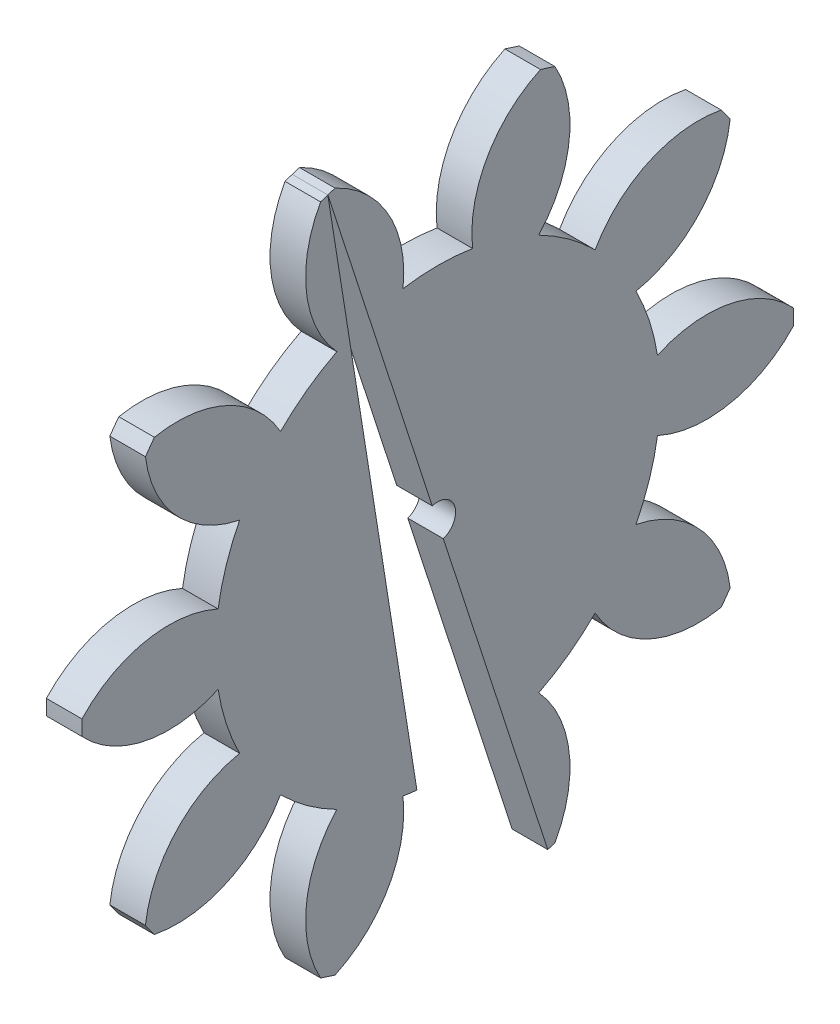
SolidWorks part; units mm, degrees
ref_plane "Plane1" through (0, 0, 0) normal (0, 0, 1) x (1, 0, 0)
ref_plane "Plane2" through (0, 0, 0) normal (0, 1, 0) x (1, 0, 0)
ref_plane "Plane3" through (0, 0, 0) normal (1, 0, 0) x (0, 0, -1)
sketch "HoldingSke" plane through (0, 0, 0) normal (0, 1, 0) x (1, 0, 0)
  line L0 (0, 0) -> (0.197, -0.0347)
  line L1 (-15, 0) -> (100, 0) construction
  line L2 (0, 0) -> (-2.1039, 2.3779)
  line L3 (0, 0) -> (-11.863, 4.5341)
  line L4 (0, 0) -> (8.5048, 1.4996)
  line L5 (0, 0) -> (-46.8476, -17.4728)
  line L6 (0, 0) -> (-2.4869, -1.6779)
  line L7 (-2.1039, 2.3779) -> (8.6586, 51.2059)
  line L8 (-76.2, 54.61) -> (-75.7, 54.61)
  line L9 (-71.009, 38.7566) -> (-53.1078, 45.2721)
  line L10 (-76.2, 71.12) -> (104.1128, 71.12)
  line L11 (0, 0) -> (-3, 0)
  line L12 (-76.2, 101.6) -> (-76.033, 101.6)
  line L13 (24.9733, 27.94) -> (52.9518, 28.4284)
  line L14 (24.9733, 27.94) -> (24.9743, 27.94)
  line L15 (24.9733, 27.94) -> (100.4006, 29.5858)
  line L16 (-63.627, -5) -> (-12.827, -5)
  circle A0 centre (0, 0) radius 1.5
  circle A1 centre (0, 0) radius 18.749
  circle A2 centre (0, 0) radius 37.5
  circle A3 centre (0, 0) radius 1.5
  dimension "MHD" = 37.498
  dimension "Hub_dia" = 75
  dimension "Bore" = 3
  dimension "MBD" = 3
  dimension "Num_teeth" = 10
  dimension "Pitch" = 0.2
  dimension "Overall_len" = 50
  dimension "Show_teeth" = 10
  dimension "Thickness" = 3
  dimension "OAL" = 50.0001
  dimension "T_dim" = 0.5
  dimension "Ap" = 20
  dimension "H" = 19.05
  dimension "Pitch_radius" = 180.3128
  dimension "Width" = 3
  dimension "Backlash" = 0.167
  dimension "Addendum_fac" = 1
  dimension "Dedendum_fac" = 1.25
  dimension "Clearance_fac" = 0.25
  dimension "Dedendum_add" = 0.001
  dimension "Module" = 5
sketch "BasProSke" plane through (0, 0, 0) normal (0, 1, 0) x (1, 0, 0)
  line L0 (-10, 0) -> (60, 0) construction
  line L1 (0, 0) -> (0, 30)
  line L2 (0, 0) -> (3, 0)
  line L3 (3, 0) -> (3, 30)
  line L4 (3, 30) -> (0, 30)
  dimension "Thickness" = 3
  dimension "Diameter" = 60
revolve "Base-Revolve" add sketch "BasProSke" angle 360 about L0
sketch "TooCutSke" plane through (0, 0, 0) normal (1, 0, 0) x (0, 0, -1)
  line L1 (0, 0) -> (0, 107) construction
  line L2 (0, 0) -> (-4.2026, 24.6442) construction
  line L3 (0, 0) -> (-15.2881, 47.0521) construction
  line L4 (-4.2026, 24.6442) -> (-7.6441, 23.526) construction
  arc A0 (2.9333, 18.5181) -> (-2.9333, 18.5181) centre (0, 0) ccw
  arc A1 (8.6913, 28.74) -> (-8.6913, 28.74) centre (0, 0) ccw
  circle A2 centre (0, 0) radius 25 construction
  circle A3 centre (0, 0) radius 23.4923 construction
  arc A4 (-2.9333, 18.5181) -> (-8.6913, 28.74) centre (-12.8686, 19.6542) ccw
  arc A5 (8.6913, 28.74) -> (2.9333, 18.5181) centre (12.8686, 19.6542) ccw
  dimension "Root_dia" = 37.498
  dimension "Overcut_dia" = 60.0508
  dimension "Pitch_dia" = 50
  dimension "Base_dia" = 46.9846
  dimension "Flank_rad" = 10
  dimension "Half_ang" = 18
  dimension "Half_CT" = 3.6186
extrude "ToothCut" cut sketch "TooCutSke" along normal through all
fillet "Breaks" [suppressed] radius 0.1
fillet "RootFillets" [suppressed] radius 1.251
pattern_circular "TeethCuts" count 10 every 36 about axis through (-10, 0, 0) along (1, 0, 0) of "ToothCut", "RootFillets", "Breaks"
sketch "HubNeaOneSke" plane through (0, 0, 0) normal (-1, 0, 0) x (0, 0, 1)
  circle A0 centre (0, 0) radius 18.749
  dimension "Diameter" = 37.498
extrude "HubNearOne" [suppressed] add sketch "HubNeaOneSke" along normal blind 47.0001
sketch "HubNeaBotSke" plane through (0, 0, 0) normal (-1, 0, 0) x (0, 0, 1)
  circle A0 centre (0, 0) radius 18.749
  dimension "Diameter" = 37.498
extrude "HubNearBoth" [suppressed] add sketch "HubNeaBotSke" along normal blind 23.5
ref_plane "FarPln" through (3, 0, 0) normal (1, 0, 0) x (0, 0, -1)
sketch "HubFarSke" plane through (3, 0, 0) normal (1, 0, 0) x (0, 0, -1)
  circle A0 centre (0, 0) radius 18.749
  dimension "Diameter" = 37.498
extrude "HubFar" [suppressed] add sketch "HubFarSke" along normal blind 23.5
sketch "BorSke" plane through (0, 0, 0) normal (1, 0, 0) x (0, 0, -1)
  circle A0 centre (0, 0) radius 1.5
  dimension "Diameter" = 3
extrude "Bore" cut sketch "BorSke" along normal mid plane 100.0001
sketch "KeySke" plane through (0, 0, 0) normal (1, 0, 0) x (0, 0, -1)
  line L0 (-0.6, 0) -> (-0.6, 2)
  line L1 (-0.6, 2) -> (0.6, 2)
  line L2 (0.6, 2) -> (0.6, 0)
  line L3 (0, 0) -> (0, 34) construction
  line L4 (-0.6, 0) -> (0.6, 0)
  dimension "Offset" = 2
  dimension "Width" = 1.2
extrude "Keyway" [suppressed] cut sketch "KeySke" along normal mid plane 100.0001
pattern_circular "Keyway2" [suppressed] count 2 every 90 about axis through (-10, 0, 0) along (1, 0, 0)
sketch "Sketch1" plane through (0, 0, 0) normal (-1, 0, 0) x (0, 0, 1)
  line L0 (-9.2705, -28.5317) -> (9.2705, 28.5317)
  line L1 (9.2705, 28.5317) -> (-1.174, -37.1089)
  line L2 (-1.174, -37.1089) -> (-9.2705, -28.5317)
  arc A0 (-9.8802, -28.3264) -> (-8.6566, -28.7239) centre (0, 0) ccw construction
  arc A1 (9.8802, 28.3264) -> (8.6566, 28.7239) centre (0, 0) ccw construction
extrude "Cut-Extrude1" cut sketch "Sketch1" against normal blind 10
equation "' \"Module@HoldingSke\" = 6.35"
equation "' \"Num_teeth@HoldingSke\" = 12"
equation "' \"Ap@HoldingSke\" =  20"
equation "' \"Ap@HoldingSke\" = 20"
equation "' \"Width@HoldingSke\" = 0.5 * 25.4"
equation "' \"Hub_dia@HoldingSke\"= 1 * 25.4"
equation "' \"Hub_dia@HoldingSke\" = 1 * 25.4"
equation "' \"Overall_len@HoldingSke\" = 1.0 * 25.4"
equation "' \"Bore@HoldingSke\" = 0.75 * 25.4"
equation "' \"T_dim@HoldingSke\" = 0.1 * 25.4"
equation "' \"Width@KeySke\" = 0.25 * 25.4"
equation "' \"Show_teeth@HoldingSke\" = 13"
equation "' \"Backlash@HoldingSke\" = 0.009 * 25.4"
equation "' \"Addendum_fac@HoldingSke\" = 1.0"
equation "' \"Dedendum_fac@HoldingSke\" = 1.25"
equation "' \"Dedendum_add@HoldingSke\" = 0.00005 * 25.4"
equation "' \"Clearance_fac@HoldingSke\" = 0.25"
equation "\"Pitch@HoldingSke\" = 1 / \"Module@HoldingSke\""
equation "\"Overcut_dia@TooCutSke\" = (\"Num_teeth@HoldingSke\" + 2 * \"Addendum_fac@HoldingSke\") / \"Pitch@HoldingSke\" + 0.002 * 25.4"
equation "\"Pitch_dia@TooCutSke\" = \"Num_teeth@HoldingSke\" / \"Pitch@HoldingSke\""
equation "\"Base_dia@TooCutSke\" = \"Num_teeth@HoldingSke\" / \"Pitch@HoldingSke\" * cos((\"Ap@HoldingSke\"  * 3.14159265 / 180))"
equation "\"Root_dia@TooCutSke\" = (\"Num_teeth@HoldingSke\" + 2) / \"Pitch@HoldingSke\" - 2 * (\"Addendum_fac@HoldingSke\" + \"Dedendum_fac@HoldingSke\") / \"Pitch@HoldingSke\" - \"Dedendum_add@HoldingSke\" * 2"
equation "\"Half_ang@TooCutSke\" = 180 / \"Num_teeth@HoldingSke\""
equation "\"Half_CT@TooCutSke\" = \"Num_teeth@HoldingSke\" / \"Pitch@HoldingSke\" * sin((3.14159265 / 2 / \"Num_teeth@HoldingSke\")) / 2 - 7 * \"Backlash@HoldingSke\" / 4"
equation "\"Flank_rad@TooCutSke\" = \"Num_teeth@HoldingSke\" / \"Pitch@HoldingSke\" / 5"
equation "\"Radius@RootFillets\" = \"Clearance_fac@HoldingSke\" / \"Pitch@HoldingSke\" + \"Dedendum_add@HoldingSke\""
equation "\"Break_rad@Breaks\" = 0.02 / \"Pitch@HoldingSke\""
equation "\"Thickness@HoldingSke\" = \"Width@HoldingSke\""
equation "\"OAL@HoldingSke\" = \"Thickness@HoldingSke\""
equation "\"MHD@HoldingSke\" = (\"Num_teeth@HoldingSke\" + 2) / \"Pitch@HoldingSke\" - 2 * (\"Addendum_fac@HoldingSke\" + \"Dedendum_fac@HoldingSke\")  / \"Pitch@HoldingSke\" - \"Dedendum_add@HoldingSke\" * 2"
equation "\"MBD@HoldingSke\" = (\"Num_teeth@HoldingSke\" + 2) / \"Pitch@HoldingSke\" - 2 * (\"Addendum_fac@HoldingSke\" + \"Dedendum_fac@HoldingSke\")  / \"Pitch@HoldingSke\" - \"Dedendum_add@HoldingSke\" * 2 - 0.002 * 25.4"
equation "\"MHD@HoldingSke\" = ((sgn( \"MHD@HoldingSke\" - \"Hub_dia@HoldingSke\" )-1)*( \"MHD@HoldingSke\" - \"Hub_dia@HoldingSke\" ))/-2+ \"Hub_dia@HoldingSke\""
equation "\"MBD@HoldingSke\" = ((sgn( \"MBD@HoldingSke\" - \"Bore@HoldingSke\" )-1)*( \"MBD@HoldingSke\" - \"Bore@HoldingSke\" ))/-2+ \"Bore@HoldingSke\""
equation "\"OAL@HoldingSke\" = ((sgn( \"OAL@HoldingSke\" - \"Overall_len@HoldingSke\" )+1)*( \"OAL@HoldingSke\" - \"Overall_len@HoldingSke\" ))/2 + \"Overall_len@HoldingSke\" + 0.000002 * 25.4"
equation "\"Num_teeth@TeethCuts\" = int( \"Show_teeth@HoldingSke\" ) + 1"
equation "\"Num_teeth@TeethCuts\" = ((sgn( \"Num_teeth@TeethCuts\" - \"Num_teeth@HoldingSke\" )-1)*( \"Num_teeth@TeethCuts\" - \"Num_teeth@HoldingSke\" ))/-2+ \"Num_teeth@HoldingSke\""
equation "\"Num_teeth@TeethCuts\" = ((sgn( \"Num_teeth@TeethCuts\" - 2.0)+1)*( \"Num_teeth@TeethCuts\" - 2.0))/2 +2.0"
equation "\"Angle@TeethCuts\" = 360.0 / \"Num_teeth@HoldingSke\""
equation "\"Diameter@BasProSke\" = (\"Num_teeth@HoldingSke\" + 2 * \"Addendum_fac@HoldingSke\") / \"Pitch@HoldingSke\""
equation "\"Thickness@BasProSke\"  = \"Thickness@HoldingSke\""
equation "' \"Fillet_rad@BasProSke\" =  \"Thickness@HoldingSke\" * 0.05"
equation "' \"Fillet_rad@BasProSke\" = \"Thickness@HoldingSke\" * 0.05"
equation "\"MHD@HoldingSke\" = ((sgn( \"MHD@HoldingSke\" - \"Root_dia@TooCutSke\" )-1)*( \"MHD@HoldingSke\" - \"Root_dia@TooCutSke\" ))/-2+ \"Root_dia@TooCutSke\""
equation "\"Diameter@HubNeaOneSke\" = \"MHD@HoldingSke\""
equation "\"Length@HubNearOne\" = \"OAL@HoldingSke\" - \"Thickness@BasProSke\""
equation "\"Diameter@HubNeaBotSke\" = \"MHD@HoldingSke\""
equation "\"Length@HubNearBoth\" = ( \"OAL@HoldingSke\" - \"Thickness@BasProSke\" ) / 2.0"
equation "\"Thickness@FarPln\" = \"Thickness@BasProSke\""
equation "\"Diameter@HubFarSke\" = \"MHD@HoldingSke\""
equation "\"Length@HubFar\" = ( \"OAL@HoldingSke\" - \"Thickness@BasProSke\" ) / 2.0"
equation "\"Diameter@BorSke\" = \"MBD@HoldingSke\""
equation "\"D1@Bore\" = \"OAL@HoldingSke\" * 2.0"
equation "\"D1@Keyway\" = \"OAL@HoldingSke\" * 2.0"
equation "\"Offset@KeySke\" = \"T_dim@HoldingSke\" + \"MBD@HoldingSke\" / 2.0"
